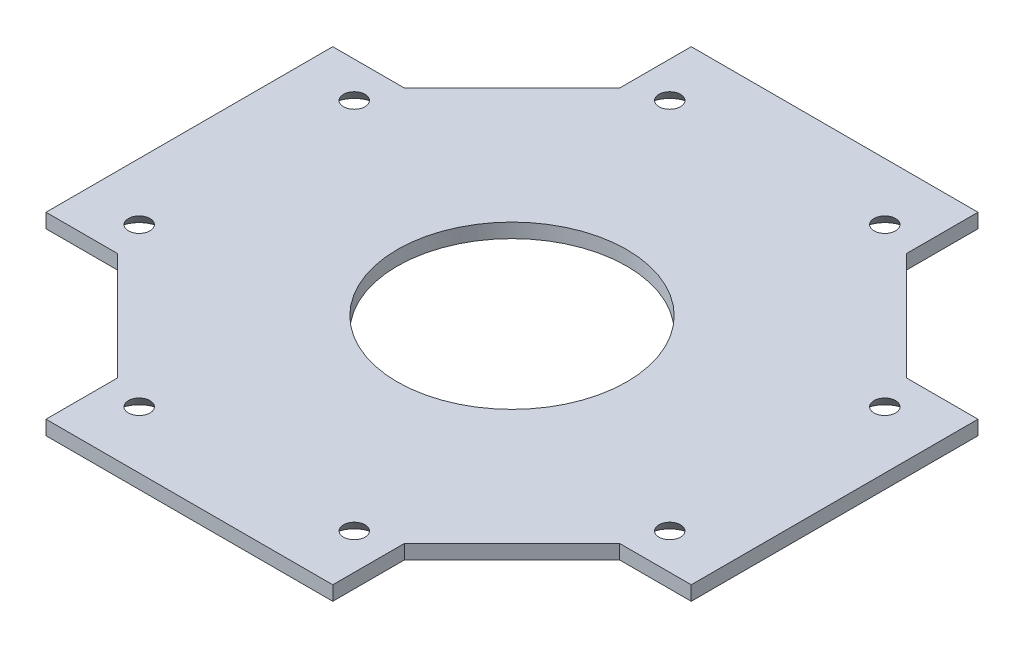
SolidWorks part; units mm, degrees
material "Plástico personalizado"
ref_plane "Plano frontal" through (0, 0, 0) normal (0, 0, 1) x (1, 0, 0)
ref_plane "Plano superior" through (0, 0, 0) normal (0, 1, 0) x (1, 0, 0)
ref_plane "Plano direito" through (0, 0, 0) normal (1, 0, 0) x (0, 0, -1)
sketch "Esboço1" plane through (0, 0, 0) normal (0, 1, 0) x (1, 0, 0)
  line L0 (-20, 35) -> (-20, 45)
  line L1 (-20, 35) -> (-35, 20)
  line L2 (-35, 20) -> (-45, 20)
  line L3 (-45, 20) -> (-45, -20)
  line L4 (-45, -20) -> (-35, -20)
  line L5 (-35, -20) -> (-20, -35)
  line L6 (-20, 45) -> (0, 45)
  line L7 (0, -45) -> (0, -16)
  line L8 (0, 16) -> (0, 45)
  line L10 (-20, -35) -> (-20, -45)
  line L11 (-20, -45) -> (0, -45)
  arc A0 (0, 16) -> (0, -16) centre (0, 0) ccw
  point P5 (-45, 0)
  dimension "D1" = 32
  dimension "D2" = 10
  dimension "D3" = 45
  dimension "D4" = 10
  dimension "D5" = 10
  dimension "D6" = 40
  dimension "D7" = 45
  dimension "D8" = 25
  dimension "D9" = 45
  dimension "D10" = 25
extrude "Ressalto-extrusão1" add sketch "Esboço1" along normal blind 2
mirror "Espelhar1" about plane through (0, 2, -16) normal (-1, 0, 0) of "Ressalto-extrusão1"
sketch "Esboço2" plane through (0, 2, 0) normal (0, 1, 0) x (1, 0, 0)
  line L0 (20, 45) -> (-20, 45) construction
  line L1 (-20, 45) -> (-20, 35) construction
  circle A0 centre (-15, 37) radius 1.5
  point P4 (-20, 40)
  dimension "D2" = 3
  dimension "D1" = 8
  dimension "D3" = 5
extrude "Corte-extrusão1" cut sketch "Esboço2" against normal through all draft 40 draft outward yes
mirror "Espelhar2" about plane through (0, 0, 0) normal (1, 0, 0) of "Corte-extrusão1"
mirror "Espelhar3" about plane through (0, 0, 0) normal (0, 0, 1) of "Espelhar2", "Corte-extrusão1"
pattern_circular "PadrãoCircular1" count 2 every 90 about axis through (0, 0, 0) along (0, 1, 0) of "Espelhar3", "Corte-extrusão1", "Espelhar2"
